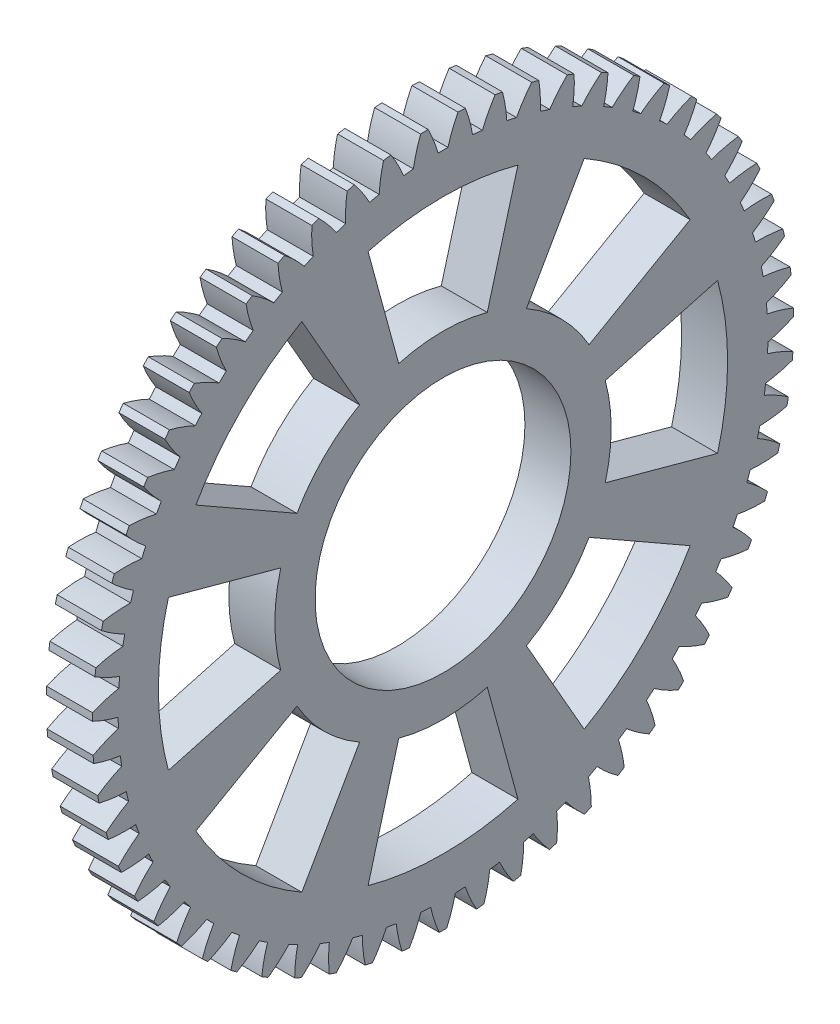
SolidWorks part; units mm, degrees
ref_plane "Plane1" through (0, 0, 0) normal (0, 0, 1) x (1, 0, 0)
ref_plane "Plane2" through (0, 0, 0) normal (0, 1, 0) x (1, 0, 0)
ref_plane "Plane3" through (0, 0, 0) normal (1, 0, 0) x (0, 0, -1)
sketch "HoldingSke" plane through (0, 0, 0) normal (0, 1, 0) x (1, 0, 0)
  line L0 (0, 0) -> (0.515, -0.8572)
  line L1 (-15, 0) -> (100, 0) construction
  line L2 (0, 0) -> (-2.1039, 2.3779)
  line L3 (0, 0) -> (-11.863, 4.5341)
  line L4 (0, 0) -> (4.4479, 7.4025)
  line L5 (0, 0) -> (-46.8476, -17.4728)
  line L6 (0, 0) -> (-3.3159, -2.2372)
  line L7 (-2.1039, 2.3779) -> (8.6586, 51.2059)
  line L8 (-76.2, 54.61) -> (-74.8, 54.61)
  line L9 (-71.009, 38.7566) -> (-53.1078, 45.2721)
  line L10 (-76.2, 71.12) -> (104.1128, 71.12)
  line L11 (0, 0) -> (-4, 0)
  line L12 (-76.2, 101.6) -> (-76.162, 101.6)
  line L13 (24.9733, 27.94) -> (52.9518, 28.4284)
  line L14 (24.9733, 27.94) -> (24.9743, 27.94)
  line L15 (24.9733, 27.94) -> (100.4006, 29.5858)
  line L16 (-63.627, -1) -> (-12.827, -1)
  circle A0 centre (0, 0) radius 4
  circle A1 centre (0, 0) radius 28.249
  circle A2 centre (0, 0) radius 37.5
  circle A3 centre (0, 0) radius 4
  dimension "MHD" = 56.498
  dimension "Hub_dia" = 75
  dimension "Bore" = 8
  dimension "MBD" = 8
  dimension "Num_teeth" = 59
  dimension "Pitch" = 1
  dimension "Overall_len" = 50
  dimension "Show_teeth" = 59
  dimension "Thickness" = 4
  dimension "OAL" = 50.0001
  dimension "T_dim" = 1.4
  dimension "Ap" = 20
  dimension "H" = 19.05
  dimension "Pitch_radius" = 180.3128
  dimension "Width" = 4
  dimension "Backlash" = 0.038
  dimension "Addendum_fac" = 1
  dimension "Dedendum_fac" = 1.25
  dimension "Clearance_fac" = 0.25
  dimension "Dedendum_add" = 0.001
  dimension "Module" = 1
sketch "BasProSke" plane through (0, 0, 0) normal (0, 1, 0) x (1, 0, 0)
  line L0 (-10, 0) -> (60, 0) construction
  line L1 (0, 0) -> (0, 30.5)
  line L2 (0, 0) -> (4, 0)
  line L3 (4, 0) -> (4, 30.5)
  line L4 (4, 30.5) -> (0, 30.5)
  dimension "Thickness" = 4
  dimension "Diameter" = 61
revolve "Base-Revolve" add sketch "BasProSke" angle 360 about L0
sketch "TooCutSke" plane through (0, 0, 0) normal (1, 0, 0) x (0, 0, -1)
  line L1 (0, 0) -> (0, 107) construction
  line L2 (0, 0) -> (-0.8518, 29.4877) construction
  line L3 (0, 0) -> (-3.1392, 58.8989) construction
  line L4 (-0.8518, 29.4877) -> (-1.5696, 29.4494) construction
  arc A0 (0.4308, 28.2457) -> (-0.4308, 28.2457) centre (0, 0) ccw
  arc A1 (1.3141, 30.4971) -> (-1.3141, 30.4971) centre (0, 0) ccw
  circle A2 centre (0, 0) radius 29.5 construction
  circle A3 centre (0, 0) radius 27.7209 construction
  arc A4 (-0.4308, 28.2457) -> (-1.3141, 30.4971) centre (-11.7994, 25.0843) ccw
  arc A5 (1.3141, 30.4971) -> (0.4308, 28.2457) centre (11.7994, 25.0843) ccw
  dimension "Root_dia" = 56.498
  dimension "Overcut_dia" = 61.0508
  dimension "Pitch_dia" = 59
  dimension "Base_dia" = 55.4419
  dimension "Flank_rad" = 11.8
  dimension "Half_ang" = 3.051
  dimension "Half_CT" = 0.7188
extrude "ToothCut" cut sketch "TooCutSke" along normal through all
fillet "Breaks" [suppressed] radius 0.02
fillet "RootFillets" [suppressed] radius 0.251
pattern_circular "TeethCuts" count 59 every 6.102 about axis through (-10, 0, 0) along (1, 0, 0) of "ToothCut", "RootFillets", "Breaks"
sketch "HubNeaOneSke" plane through (0, 0, 0) normal (-1, 0, 0) x (0, 0, 1)
  circle A0 centre (0, 0) radius 28.249
  dimension "Diameter" = 56.498
extrude "HubNearOne" [suppressed] add sketch "HubNeaOneSke" along normal blind 46.0001
sketch "HubNeaBotSke" plane through (0, 0, 0) normal (-1, 0, 0) x (0, 0, 1)
  circle A0 centre (0, 0) radius 28.249
  dimension "Diameter" = 56.498
extrude "HubNearBoth" [suppressed] add sketch "HubNeaBotSke" along normal blind 23
ref_plane "FarPln" through (4, 0, 0) normal (1, 0, 0) x (0, 0, -1)
sketch "HubFarSke" plane through (4, 0, 0) normal (1, 0, 0) x (0, 0, -1)
  circle A0 centre (0, 0) radius 28.249
  dimension "Diameter" = 56.498
extrude "HubFar" [suppressed] add sketch "HubFarSke" along normal blind 23
sketch "BorSke" plane through (0, 0, 0) normal (1, 0, 0) x (0, 0, -1)
  circle A0 centre (0, 0) radius 4
  dimension "Diameter" = 8
extrude "Bore" cut sketch "BorSke" along normal mid plane 100.0001
sketch "KeySke" plane through (0, 0, 0) normal (1, 0, 0) x (0, 0, -1)
  line L0 (-1.5, 0) -> (-1.5, 5.4)
  line L1 (-1.5, 5.4) -> (1.5, 5.4)
  line L2 (1.5, 5.4) -> (1.5, 0)
  line L3 (0, 0) -> (0, 34) construction
  line L4 (-1.5, 0) -> (1.5, 0)
  dimension "Offset" = 5.4
  dimension "Width" = 3
extrude "Keyway" [suppressed] cut sketch "KeySke" along normal mid plane 100.0001
pattern_circular "Keyway2" [suppressed] count 2 every 90 about axis through (-10, 0, 0) along (1, 0, 0)
sketch "Sketch1" plane through (4, 0, 0) normal (1, 0, 0) x (0, 0, -1)
  circle A0 centre (0, 0) radius 11.125
  dimension "D1" = 22.25
extrude "Cut-Extrude1" cut sketch "Sketch1" against normal blind 10
sketch "Sketch2" plane through (4, 0, 0) normal (1, 0, 0) x (0, 0, -1)
  line L0 (0, 14.625) -> (0, 24.749) construction
  line L1 (3.8504, 14.109) -> (6.5158, 23.8759)
  line L2 (-3.8504, 14.109) -> (-6.5158, 23.8759)
  line L3 (7.0263, 12.6383) -> (12.0478, 21.4292)
  line L4 (12.4716, 7.193) -> (21.2625, 12.2145)
  line L5 (13.6773, 3.9073) -> (23.4442, 6.5726)
  line L6 (13.6773, -3.7935) -> (23.4442, -6.4589)
  line L7 (12.2066, -6.9694) -> (20.9975, -11.9909)
  line L8 (6.7613, -12.4147) -> (11.7828, -21.2056)
  line L9 (3.4756, -13.6204) -> (6.1409, -23.3873)
  line L10 (-4.2252, -13.6204) -> (-6.8906, -23.3873)
  line L11 (-7.4011, -12.1497) -> (-12.4226, -20.9406)
  line L12 (-12.8464, -6.7044) -> (-21.6373, -11.7259)
  line L13 (-14.0521, -3.4187) -> (-23.819, -6.084)
  line L14 (-14.0521, 4.2821) -> (-23.819, 6.9475)
  line L15 (-12.5814, 7.458) -> (-21.3723, 12.4795)
  line L16 (-7.1361, 12.9033) -> (-12.1576, 21.6942)
  circle A0 centre (0, 0) radius 14.625
  circle A1 centre (0, 0) radius 11.125 construction
  circle A2 centre (0, 0) radius 24.749
  arc A3 (-26.9187, 8.5668) -> (-27.1674, 7.7419) centre (0, 0) ccw construction
  point P15 (0, 0)
  point P16 (0, 0)
  point P17 (0, 0)
  point P46 (-0.1874, 0.2443)
  point P47 (0, 0)
  point P48 (0, 0)
  dimension "D1" = 3.5
  dimension "D2" = 3.5
  dimension "D4" = 3.5
  dimension "D3" = 8
extrude "Cut-Extrude2" cut sketch "Sketch2" against normal blind 10 contours A0 L0 A2 L2 | L0 A0 L1 A2
pattern_circular "CirPattern1" count 8 over 360 about axis through (0, 0, 0) along (1, 0, 0) of "Cut-Extrude2"
equation "' \"Module@HoldingSke\" = 6.35"
equation "' \"Num_teeth@HoldingSke\" = 12"
equation "' \"Ap@HoldingSke\" =  20"
equation "' \"Ap@HoldingSke\" = 20"
equation "' \"Width@HoldingSke\" = 0.5 * 25.4"
equation "' \"Hub_dia@HoldingSke\"= 1 * 25.4"
equation "' \"Hub_dia@HoldingSke\" = 1 * 25.4"
equation "' \"Overall_len@HoldingSke\" = 1.0 * 25.4"
equation "' \"Bore@HoldingSke\" = 0.75 * 25.4"
equation "' \"T_dim@HoldingSke\" = 0.1 * 25.4"
equation "' \"Width@KeySke\" = 0.25 * 25.4"
equation "' \"Show_teeth@HoldingSke\" = 13"
equation "' \"Backlash@HoldingSke\" = 0.009 * 25.4"
equation "' \"Addendum_fac@HoldingSke\" = 1.0"
equation "' \"Dedendum_fac@HoldingSke\" = 1.25"
equation "' \"Dedendum_add@HoldingSke\" = 0.00005 * 25.4"
equation "' \"Clearance_fac@HoldingSke\" = 0.25"
equation "\"Pitch@HoldingSke\" = 1 / \"Module@HoldingSke\""
equation "\"Overcut_dia@TooCutSke\" = (\"Num_teeth@HoldingSke\" + 2 * \"Addendum_fac@HoldingSke\") / \"Pitch@HoldingSke\" + 0.002 * 25.4"
equation "\"Pitch_dia@TooCutSke\" = \"Num_teeth@HoldingSke\" / \"Pitch@HoldingSke\""
equation "\"Base_dia@TooCutSke\" = \"Num_teeth@HoldingSke\" / \"Pitch@HoldingSke\" * cos((\"Ap@HoldingSke\"  * 3.14159265 / 180))"
equation "\"Root_dia@TooCutSke\" = (\"Num_teeth@HoldingSke\" + 2) / \"Pitch@HoldingSke\" - 2 * (\"Addendum_fac@HoldingSke\" + \"Dedendum_fac@HoldingSke\") / \"Pitch@HoldingSke\" - \"Dedendum_add@HoldingSke\" * 2"
equation "\"Half_ang@TooCutSke\" = 180 / \"Num_teeth@HoldingSke\""
equation "\"Half_CT@TooCutSke\" = \"Num_teeth@HoldingSke\" / \"Pitch@HoldingSke\" * sin((3.14159265 / 2 / \"Num_teeth@HoldingSke\")) / 2 - 7 * \"Backlash@HoldingSke\" / 4"
equation "\"Flank_rad@TooCutSke\" = \"Num_teeth@HoldingSke\" / \"Pitch@HoldingSke\" / 5"
equation "\"Radius@RootFillets\" = \"Clearance_fac@HoldingSke\" / \"Pitch@HoldingSke\" + \"Dedendum_add@HoldingSke\""
equation "\"Break_rad@Breaks\" = 0.02 / \"Pitch@HoldingSke\""
equation "\"Thickness@HoldingSke\" = \"Width@HoldingSke\""
equation "\"OAL@HoldingSke\" = \"Thickness@HoldingSke\""
equation "\"MHD@HoldingSke\" = (\"Num_teeth@HoldingSke\" + 2) / \"Pitch@HoldingSke\" - 2 * (\"Addendum_fac@HoldingSke\" + \"Dedendum_fac@HoldingSke\")  / \"Pitch@HoldingSke\" - \"Dedendum_add@HoldingSke\" * 2"
equation "\"MBD@HoldingSke\" = (\"Num_teeth@HoldingSke\" + 2) / \"Pitch@HoldingSke\" - 2 * (\"Addendum_fac@HoldingSke\" + \"Dedendum_fac@HoldingSke\")  / \"Pitch@HoldingSke\" - \"Dedendum_add@HoldingSke\" * 2 - 0.002 * 25.4"
equation "\"MHD@HoldingSke\" = ((sgn( \"MHD@HoldingSke\" - \"Hub_dia@HoldingSke\" )-1)*( \"MHD@HoldingSke\" - \"Hub_dia@HoldingSke\" ))/-2+ \"Hub_dia@HoldingSke\""
equation "\"MBD@HoldingSke\" = ((sgn( \"MBD@HoldingSke\" - \"Bore@HoldingSke\" )-1)*( \"MBD@HoldingSke\" - \"Bore@HoldingSke\" ))/-2+ \"Bore@HoldingSke\""
equation "\"OAL@HoldingSke\" = ((sgn( \"OAL@HoldingSke\" - \"Overall_len@HoldingSke\" )+1)*( \"OAL@HoldingSke\" - \"Overall_len@HoldingSke\" ))/2 + \"Overall_len@HoldingSke\" + 0.000002 * 25.4"
equation "\"Num_teeth@TeethCuts\" = int( \"Show_teeth@HoldingSke\" ) + 1"
equation "\"Num_teeth@TeethCuts\" = ((sgn( \"Num_teeth@TeethCuts\" - \"Num_teeth@HoldingSke\" )-1)*( \"Num_teeth@TeethCuts\" - \"Num_teeth@HoldingSke\" ))/-2+ \"Num_teeth@HoldingSke\""
equation "\"Num_teeth@TeethCuts\" = ((sgn( \"Num_teeth@TeethCuts\" - 2.0)+1)*( \"Num_teeth@TeethCuts\" - 2.0))/2 +2.0"
equation "\"Angle@TeethCuts\" = 360.0 / \"Num_teeth@HoldingSke\""
equation "\"Diameter@BasProSke\" = (\"Num_teeth@HoldingSke\" + 2 * \"Addendum_fac@HoldingSke\") / \"Pitch@HoldingSke\""
equation "\"Thickness@BasProSke\"  = \"Thickness@HoldingSke\""
equation "' \"Fillet_rad@BasProSke\" =  \"Thickness@HoldingSke\" * 0.05"
equation "' \"Fillet_rad@BasProSke\" = \"Thickness@HoldingSke\" * 0.05"
equation "\"MHD@HoldingSke\" = ((sgn( \"MHD@HoldingSke\" - \"Root_dia@TooCutSke\" )-1)*( \"MHD@HoldingSke\" - \"Root_dia@TooCutSke\" ))/-2+ \"Root_dia@TooCutSke\""
equation "\"Diameter@HubNeaOneSke\" = \"MHD@HoldingSke\""
equation "\"Length@HubNearOne\" = \"OAL@HoldingSke\" - \"Thickness@BasProSke\""
equation "\"Diameter@HubNeaBotSke\" = \"MHD@HoldingSke\""
equation "\"Length@HubNearBoth\" = ( \"OAL@HoldingSke\" - \"Thickness@BasProSke\" ) / 2.0"
equation "\"Thickness@FarPln\" = \"Thickness@BasProSke\""
equation "\"Diameter@HubFarSke\" = \"MHD@HoldingSke\""
equation "\"Length@HubFar\" = ( \"OAL@HoldingSke\" - \"Thickness@BasProSke\" ) / 2.0"
equation "\"Diameter@BorSke\" = \"MBD@HoldingSke\""
equation "\"D1@Bore\" = \"OAL@HoldingSke\" * 2.0"
equation "\"D1@Keyway\" = \"OAL@HoldingSke\" * 2.0"
equation "\"Offset@KeySke\" = \"T_dim@HoldingSke\" + \"MBD@HoldingSke\" / 2.0"
